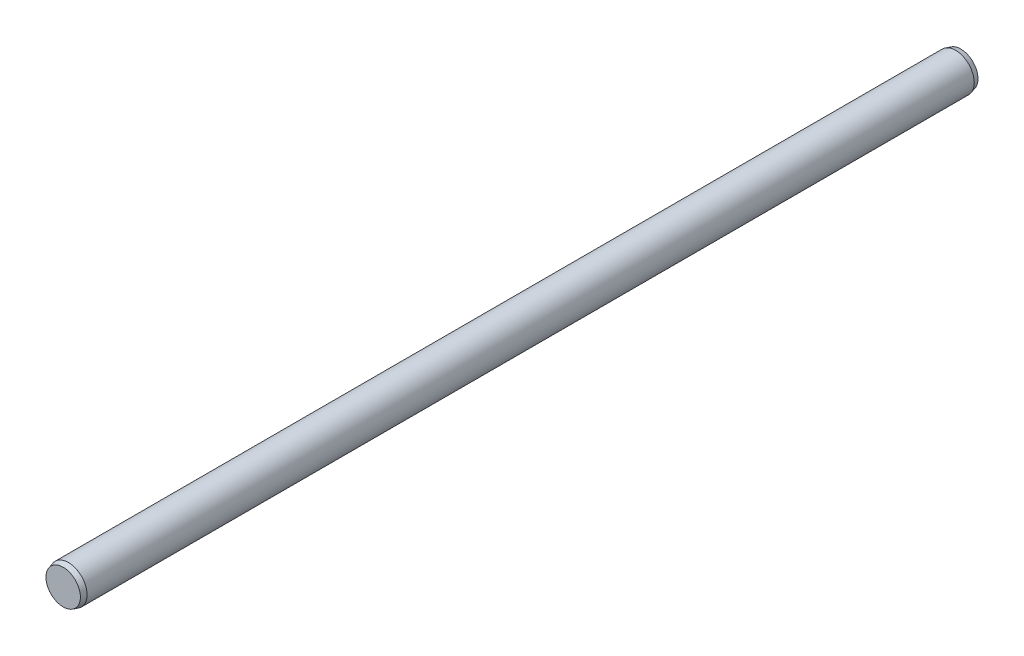
SolidWorks part; units mm, degrees
ref_plane "Front Plane" through (0, 0, 0) normal (0, 0, 1) x (1, 0, 0)
ref_plane "Top Plane" through (0, 0, 0) normal (0, 1, 0) x (1, 0, 0)
ref_plane "Right Plane" through (0, 0, 0) normal (1, 0, 0) x (0, 0, -1)
sketch "Sketch1" plane through (0, 0, 0) normal (0, 0, 1) x (1, 0, 0)
  circle A0 centre (0, 0) radius 3.175
  point P3 (0, 3.175)
  dimension "Diameter" = 6.35
sketch "Sketch2" plane through (0, 0, 0) normal (1, 0, 0) x (0, 0, -1)
  line L0 (-76.2, 0) -> (76.2, 0) construction
  line L1 (-76.2, 0) -> (-76.2, 3.175)
  line L2 (-76.2, 3.175) -> (76.2, 3.175)
  line L3 (76.2, 3.175) -> (76.2, 0)
  line L4 (-76.2, 2.921) -> (-75.3142, 3.175)
  line L5 (76.2, 2.921) -> (75.3142, 3.175)
  dimension "Length" = 152.4
  dimension "Chamfer Angle" = 16
  dimension "Point Diameter" = 5.842
sketch "Sketch3" plane through (0, 0, 0) normal (1, 0, 0) x (0, 0, -1)
  line L0 (-76.2, 0) -> (76.2, 0) construction
  line L1 (76.2, 3.175) -> (76.2, 0) construction
  line L2 (-76.2, 3.175) -> (76.2, 3.175) construction
  line L3 (-76.2, 0) -> (-76.2, 3.175) construction
  line L4 (-76.2, 0) -> (76.2, 0)
  line L5 (76.2, 2.921) -> (76.2, 0)
  line L6 (-75.3142, 3.175) -> (75.3142, 3.175)
  line L7 (-76.2, 0) -> (-76.2, 2.921)
  line L8 (76.2, 2.921) -> (75.3142, 3.175) construction
  line L9 (-76.2, 2.921) -> (-75.3142, 3.175) construction
  line L10 (76.2, 2.921) -> (75.3142, 3.175)
  line L11 (-76.2, 2.921) -> (-75.3142, 3.175)
revolve "Revolve1" add sketch "Sketch3" angle 360 about L0
